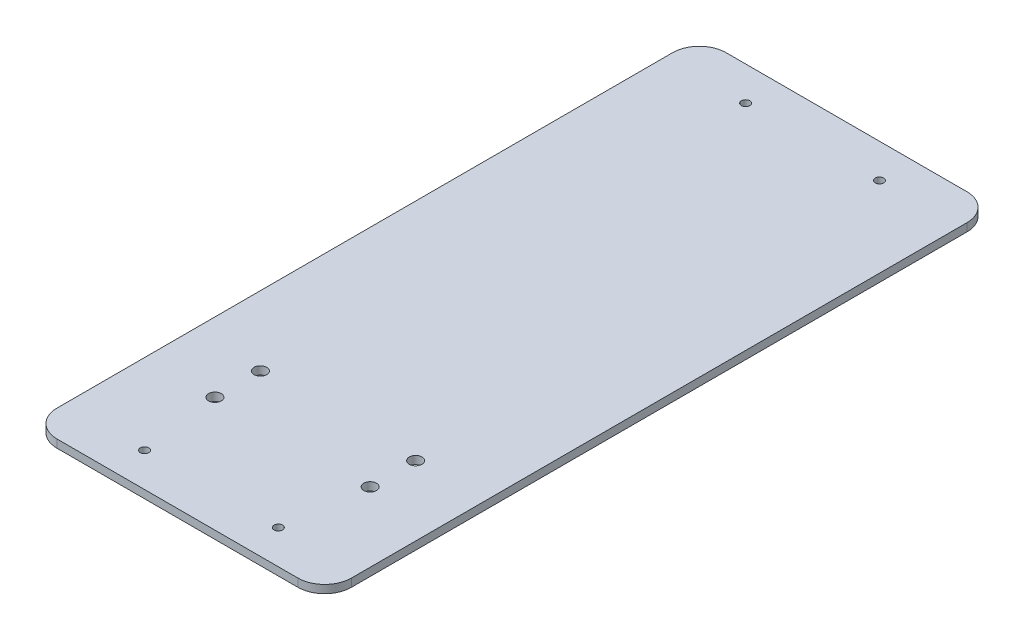
SolidWorks part; units mm, degrees
ref_plane "Alzado" through (0, 0, 0) normal (0, 0, 1) x (1, 0, 0)
ref_plane "Planta" through (0, 0, 0) normal (0, 1, 0) x (1, 0, 0)
ref_plane "Vista lateral" through (0, 0, 0) normal (1, 0, 0) x (0, 0, -1)
sketch "Croquis1" plane through (0, 0, 0) normal (0, 1, 0) x (1, 0, 0)
  line L1 (10, 0) -> (100, 0)
  line L2 (0, 10) -> (0, 240)
  line L3 (10, 250) -> (100, 250)
  line L4 (110, 10) -> (110, 240)
  arc A0 (100, 0) -> (110, 10) centre (100, 10) ccw
  arc A1 (10, 0) -> (0, 10) centre (10, 10) cw
  arc A2 (0, 240) -> (10, 250) centre (10, 240) cw
  arc A3 (100, 250) -> (110, 240) centre (100, 240) cw
  point P7 (110, 0)
  point P10 (0, 0)
  point P15 (110, 250)
  dimension "D3" = 10
  dimension "D1" = 250
  dimension "D2" = 110
extrude "Saliente-Extruir1" add sketch "Croquis1" along normal blind 3
sketch "Croquis2" plane through (0, 3, 0) normal (0, 1, 0) x (1, 0, 0)
  line L0 (10, 0) -> (100, 0) construction
  line L1 (30, 12.7) -> (80, 12.7) construction
  line L2 (30, 237.3) -> (80, 237.3) construction
  line L3 (100, 250) -> (10, 250) construction
  line L4 (55, 250) -> (55, 237.3) construction
  circle A0 centre (30, 237.3) radius 1.5875
  circle A1 centre (80, 237.3) radius 1.5875
  circle A2 centre (30, 12.7) radius 1.5875
  circle A3 centre (80, 12.7) radius 1.5875
  point P8 (55, 0)
  point P11 (55, 12.7)
  point P14 (55, 237.3)
  dimension "D1" = 3.175
  dimension "D2" = 3.175
  dimension "D3" = 3.175
  dimension "D4" = 3.175
  dimension "D5" = 12.7
  dimension "D6" = 50
  dimension "D7" = 12.7
  dimension "D8" = 50
extrude "Cortar-Extruir1" cut sketch "Croquis2" against normal blind 20
sketch "Croquis3" plane through (0, 3, 0) normal (0, 1, 0) x (1, 0, 0)
  line L0 (100, 250) -> (10, 250) construction
  line L1 (20, 77) -> (90, 77) construction
  line L2 (20, 77) -> (20, 37) construction
  line L3 (20, 37) -> (90, 37) construction
  line L4 (90, 77) -> (90, 37) construction
  line L5 (26, 60) -> (26, 43) construction
  line L6 (26, 60) -> (84, 60) construction
  line L7 (10, 0) -> (100, 0) construction
  circle A0 centre (26, 60) radius 2.3813
  circle A1 centre (84, 60) radius 2.3813
  circle A2 centre (26, 43) radius 2.3813
  circle A3 centre (84, 43) radius 2.3813
  point P4 (55, 77)
  point P7 (55, 250)
  point P16 (55, 60)
  dimension "D4" = 4.7625
  dimension "D1" = 40
  dimension "D2" = 70
  dimension "D3" = 37
  dimension "D5" = 58
  dimension "D6" = 17
  dimension "D7" = 6
extrude "Cortar-Extruir2" cut sketch "Croquis3" against normal blind 10
